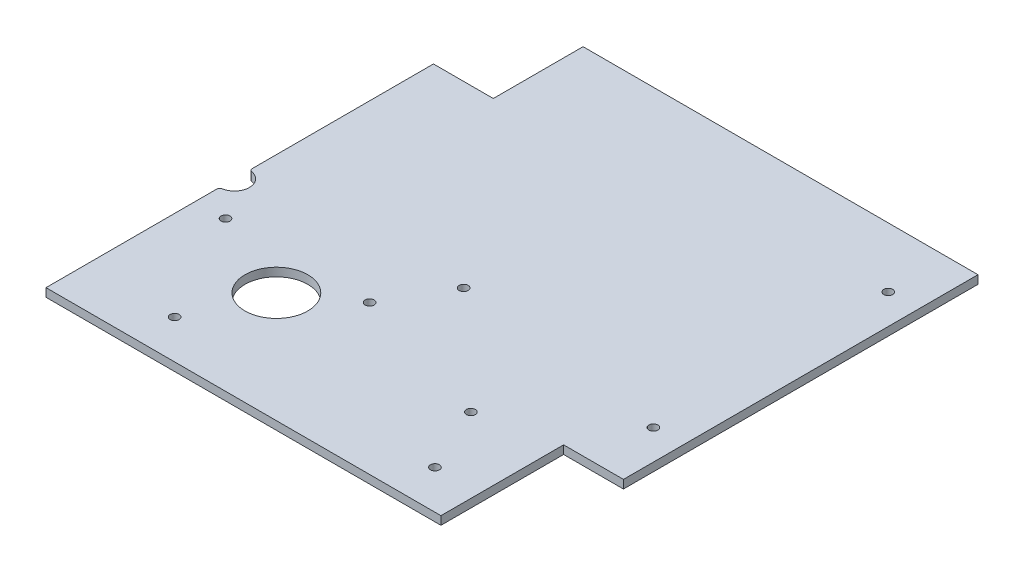
SolidWorks part; units mm, degrees
ref_plane "Front" through (0, 0, 0) normal (0, 0, 1) x (1, 0, 0)
ref_plane "Top" through (0, 0, 0) normal (0, 1, 0) x (1, 0, 0)
ref_plane "Right" through (0, 0, 0) normal (1, 0, 0) x (0, 0, -1)
sketch "Sketch1" plane through (0, 0, 0) normal (0, 1, 0) x (1, 0, 0)
  line L0 (56, -79.75) -> (56, -38.75)
  line L1 (-76, -79.75) -> (76, -79.75)
  line L2 (-76, -79.75) -> (-76, 79.75)
  line L3 (-76, 79.75) -> (76, 79.75)
  line L4 (76, -79.75) -> (76, 79.75)
  line L5 (-76, -79.75) -> (76, 79.75) construction
  line L6 (-76, 79.75) -> (76, -79.75) construction
  line L7 (56, -38.75) -> (76, -38.75)
  line L9 (-76, 79.75) -> (-56, 79.75)
  line L10 (-76, 79.75) -> (-76, 49.75)
  line L11 (-76, 49.75) -> (-56, 49.75)
  line L12 (-56, 79.75) -> (-56, 49.75)
  line L13 (-76, 79.75) -> (-56, 49.75) construction
  line L14 (-76, 49.75) -> (-56, 79.75) construction
  circle A0 centre (-66, -29.75) radius 1.5
  circle A1 centre (41, -66.75) radius 1.5
  circle A2 centre (-46, -66.75) radius 1.5
  circle A3 centre (66, 59.75) radius 1.5
  circle A4 centre (66, -18.75) radius 1.5
  point P0 (0, 0)
  point P13 (-66, 64.75)
  dimension "D7" = 3
  dimension "D8" = 10
  dimension "D9" = 50
  dimension "D10" = 3
  dimension "D11" = 3
  dimension "D12" = 15
  dimension "D13" = 13
  dimension "D14" = 30
  dimension "D15" = 3
  dimension "D16" = 3
  dimension "D17" = 10
  dimension "D18" = 20
  dimension "D1" = 159.5
  dimension "D2" = 152
  dimension "D3" = 41
  dimension "D4" = 20
  dimension "D5" = 30
  dimension "D6" = 20
  dimension "D19" = 20
extrude "Boss-Extrude1" add sketch "Sketch1" along normal blind 2.8 contours L3 L12 L11 L2 L1 L0 L7 L4 A4 A3 A2 A1 A0
sketch "Sketch2" plane through (0, 2.8, 0) normal (0, 1, 0) x (1, 0, 0)
  line L0 (31, -44.75) -> (-11.8683, -20) construction
  line L1 (-17.6183, -29.9593) -> (-6.1183, -10.0407) construction
  line L2 (-76, -79.75) -> (56, -79.75) construction
  line L3 (56, -79.75) -> (56, -38.75) construction
  circle A0 centre (31, -44.75) radius 1.5
  circle A1 centre (-6.1183, -10.0407) radius 1.5
  circle A2 centre (-17.6183, -29.9593) radius 1.5
  dimension "D1" = 3
  dimension "D3" = 23
  dimension "D7" = 3
  dimension "D8" = 3
  dimension "D2" = 49.5
  dimension "D4" = 30
  dimension "D5" = 35
  dimension "D6" = 25
extrude "Cut-Extrude1" cut sketch "Sketch2" against normal up to next
sketch "Sketch3" plane through (0, 2.8, 0) normal (0, 1, 0) x (1, 0, 0)
  line L0 (-76, -79.75) -> (56, -79.75) construction
  line L1 (-76, -79.75) -> (-76, 49.75) construction
  circle A0 centre (-36, -42.75) radius 10.5
  dimension "D1" = 21
  dimension "D3" = 40
  dimension "D2" = 37
extrude "Cut-Extrude2" cut sketch "Sketch3" against normal up to next
sketch "Sketch4" plane through (0, 2.8, 0) normal (0, 1, 0) x (1, 0, 0)
  line L0 (-76, -79.75) -> (-76, 49.75) construction
  line L1 (-76, -79.75) -> (56, -79.75) construction
  circle A0 centre (-76, -16.75) radius 5
  dimension "D1" = 10
  dimension "D2" = 63
extrude "Cut-Extrude3" cut sketch "Sketch4" against normal up to next
fillet "Fillet1" radius 1 2 edges at (-76, 1.4, 11.75) (-76, 1.4, 21.75)
